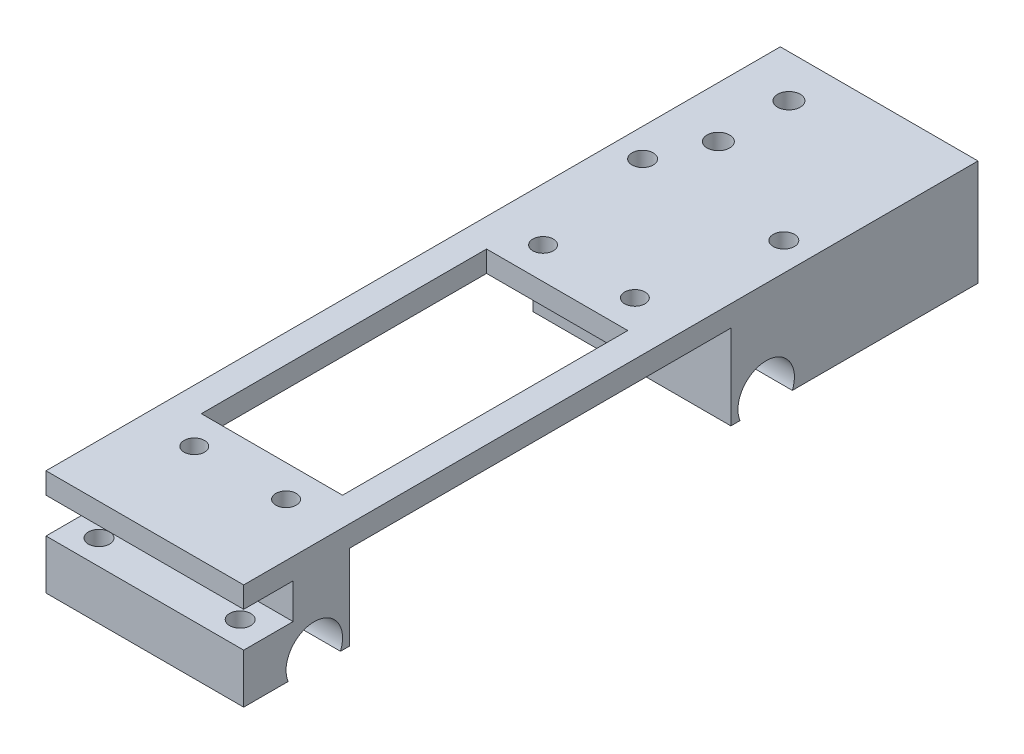
SolidWorks part; units mm, degrees
ref_plane "Front Plane" through (0, 0, 0) normal (0, 0, 1) x (1, 0, 0)
ref_plane "Top Plane" through (0, 0, 0) normal (0, 1, 0) x (1, 0, 0)
ref_plane "Right Plane" through (0, 0, 0) normal (1, 0, 0) x (0, 0, -1)
sketch "Sketch1" plane through (0, 0, 0) normal (0, 1, 0) x (1, 0, 0)
  line L1 (0, 0) -> (28, 0)
  line L2 (0, 0) -> (0, 84)
  line L3 (0, 84) -> (28, 84)
  line L4 (28, 0) -> (28, 84)
  dimension "D1" = 84
  dimension "D2" = 28
extrude "Boss-Extrude2" add sketch "Sketch1" along normal blind 15
sketch "Sketch7" plane through (28, 0, 0) normal (1, 0, 0) x (0, 0, -1)
  line L0 (46, -8.0129) -> (46, 21.5852) construction
  line L1 (84, 15) -> (84, 0) construction
  line L7 (0, 0) -> (84, 0) construction
  line L8 (15, 0) -> (69, 0)
  line L9 (15, 0) -> (15, 12)
  line L10 (15, 12) -> (69, 12)
  line L11 (69, 0) -> (69, 12)
  dimension "D1" = 38
  dimension "D2" = 12
  dimension "D3" = 54
  dimension "D4" = 23
extrude "Cut-Extrude2" cut sketch "Sketch7" against normal through all both and the other way through all
sketch "Sketch6" plane through (0, 15, 0) normal (0, 1, 0) x (1, 0, 0)
  line L0 (28, 0) -> (28, 84) construction
  line L1 (4, 18) -> (24, 18)
  line L2 (4, 18) -> (4, 58.4)
  line L3 (4, 58.4) -> (24, 58.4)
  line L4 (24, 18) -> (24, 58.4)
  line L5 (0, 0) -> (28, 0) construction
  line L6 (14, 76.1145) -> (14, -1.6161) construction
  line L7 (-14.9383, 38.2) -> (53.8018, 38.2) construction
  dimension "D1" = 40.4
  dimension "D2" = 4
  dimension "D3" = 20
  dimension "D4" = 18
  dimension "D5" = 10
  dimension "D6" = 20.2
extrude "Cut-Extrude1" cut sketch "Sketch6" against normal through all
sketch "Sketch8" plane through (0, 0, 0) normal (0, 0, 1) x (1, 0, 0)
  line L0 (0, 15) -> (0, 0) construction
  line L1 (0, 12) -> (28, 12)
  line L2 (0, 12) -> (0, 7)
  line L3 (0, 7) -> (28, 7)
  line L4 (28, 12) -> (28, 7)
  line L5 (28, 15) -> (28, 0) construction
  line L7 (0, 15) -> (28, 15) construction
  dimension "D1" = 5
  dimension "D2" = 3
extrude "Cut-Extrude3" cut sketch "Sketch8" against normal blind 7
sketch "Sketch9" plane through (0, 15, 0) normal (0, 1, 0) x (1, 0, 0)
  line L0 (0, 0) -> (0, 84) construction
  line L1 (14, -7.4352) -> (14, 63.0978) construction
  line L2 (-18.7571, 38.2) -> (45.0506, 38.2) construction
  line L3 (24, 18) -> (24, 58.4) construction
  line L4 (24, 58.4) -> (4, 58.4) construction
  line L8 (4, 18) -> (24, 18) construction
  circle A0 centre (7.5, 13.5) radius 1.45
  circle A1 centre (20.5, 13.5) radius 1.45
  circle A2 centre (7.5, 62.9) radius 1.45
  circle A3 centre (20.5, 62.9) radius 1.45
  dimension "D1" = 2.9
  dimension "D2" = 7.5
  dimension "D3" = 10
  dimension "D4" = 20.2
  dimension "D5" = 4.5
extrude "Cut-Extrude4" cut sketch "Sketch9" against normal blind 6
sketch "Sketch11" plane through (0, 0, 0) normal (-1, 0, 0) x (0, 0, 1)
  line L0 (0, 0) -> (-15, 0) construction
  line L1 (-40, -19.5654) -> (-40, 29.1754) construction
  line L2 (0, 7) -> (0, 0) construction
  line L3 (0, 15) -> (0, 12) construction
  line L5 (-69, 0) -> (-69, 12) construction
  circle A1 centre (-10, 1.5) radius 4
  circle A4 centre (-74, 1.5) radius 4
  dimension "D1" = 8
  dimension "D5" = 8
  dimension "D2" = 10
  dimension "D3" = 1.5
  dimension "D4" = 40
  dimension "D6" = 5
extrude "Cut-Extrude5" cut sketch "Sketch11" against normal through all both and the other way through all
sketch "Sketch12" plane through (0, 0, 0) normal (0, -1, 0) x (1, 0, 0)
  line L0 (0, 0) -> (0, -6.2919) construction
  line L1 (0, 0) -> (28, 0) construction
  line L2 (14, 8.2671) -> (14, -46) construction
  line L3 (28, 0) -> (28, -6.2919) construction
  line L4 (-11.0529, -46) -> (44.1232, -46) construction
  line L5 (0, -84) -> (28, -84) construction
  circle A0 centre (4, -3.5) radius 1.5
  circle A1 centre (24, -3.5) radius 1.5
  dimension "D1" = 3
  dimension "D2" = 4
  dimension "D3" = 3.5
  dimension "D4" = 14
  dimension "D5" = 38
extrude "Cut-Extrude6" cut sketch "Sketch12" against normal blind 8
sketch "Sketch13" plane through (0, 0, 0) normal (0, -1, 0) x (1, 0, 0)
  line L0 (0, -77.7081) -> (0, -84) construction
  line L1 (28, -77.7081) -> (28, -84) construction
  line L2 (0, -84) -> (28, -84) construction
  circle A0 centre (4, -80.5) radius 1.5
  circle A1 centre (24, -80.5) radius 1.5
  circle A2 centre (4, -3.5) radius 1.5 construction
  dimension "D1" = 4
  dimension "D2" = 4
  dimension "D3" = 3.5
extrude "Cut-Extrude7" cut sketch "Sketch13" against normal through all
sketch "Sketch15" plane through (0, 0, -84) normal (0, 0, -1) x (-1, 0, 0)
  line L0 (0, 15) -> (-28, 15) construction
  line L5 (0, 0) -> (-28, 0) construction
  line L6 (-28, 15) -> (0, 15)
  line L7 (0, 15) -> (0, 0) construction
  line L8 (-28, 15) -> (-28, 0)
  line L9 (-28, 0) -> (0, 0)
  line L10 (0, 15) -> (0, 8.75)
  line L11 (-10.4665, 5.6254) -> (-17.5062, 5.5747)
  line L12 (0, 6.5) -> (0, 0)
  line L13 (0, 8.75) -> (-10.2003, 8.75)
  line L15 (0, 6.5) -> (-10.127, 6.5)
  arc A0 (-10.4665, 5.6254) -> (-10.127, 6.5) centre (-14, 7.5) ccw
  arc A1 (-10.2003, 8.75) -> (-17.5062, 5.5747) centre (-14, 7.5) ccw
  dimension "D3" = 8
  dimension "D6" = 1.9
  dimension "D1" = 7.5
  dimension "D2" = 14
  dimension "D4" = 14
  dimension "D5" = 28
  dimension "D7" = 1
  dimension "D8" = 15
extrude "Boss-Extrude3" add sketch "Sketch15" along normal blind 20
sketch "Sketch17" plane through (0, 0, -104) normal (0, 0, -1) x (-1, 0, 0)
  line L0 (0, 8.75) -> (-10.2003, 8.75)
  line L1 (-17.5062, 5.5747) -> (-10.4665, 5.6254)
  line L2 (-10.4665, 5.6254) -> (-17.5062, 5.5747) construction
  line L3 (-10.4665, 5.6254) -> (-17.5062, 5.5747) construction
  line L4 (0, 6.5) -> (-10.127, 6.5)
  line L5 (0, 6.5) -> (0, 8.75)
  arc A0 (-17.5062, 5.5747) -> (-10.2003, 8.75) centre (-14, 7.5) cw
  arc A1 (-10.4665, 5.6254) -> (-10.127, 6.5) centre (-14, 7.5) ccw
extrude "Cut-Extrude10" cut sketch "Sketch17" against normal blind 25
hole_wizard "CBORE for M3 Hex Socket Head Cap Screw1" positions "3DSketch1" profile "Sketch20" counterbore size "M3" standard "ISO" end condition through all
sketch3d "3DSketch1"
  line L0 (28, 0, -104) -> (0, 0, -104) construction
  point P0 (7.2263, 0, -88)
  point P2 (7.2263, 0, -98)
  dimension "D1" = 10
  dimension "D2" = 6
sketch "Sketch20" plane through (7.2263, 0, -88) normal (1, 0, 0) x (0, 0, -1)
  line L0 (0, 0) -> (0, 15)
  line L1 (0, 15) -> (1.6, 15)
  line L3 (1.6, 15) -> (1.6, 3.4)
  line L4 (1.6, 3.4) -> (3.25, 3.4)
  line L5 (3.25, 3.4) -> (3.25, 0)
  line L7 (3.25, 0) -> (0, 0)
  line L11 (0, -6.35) -> (0, 107.95) construction
  dimension "Thru Hole Dia." = 3.2
  dimension "Thru Hole Depth" = 15
  dimension "C'Bore Dia." = 6.5
  dimension "C'Bore Depth" = 3.4
